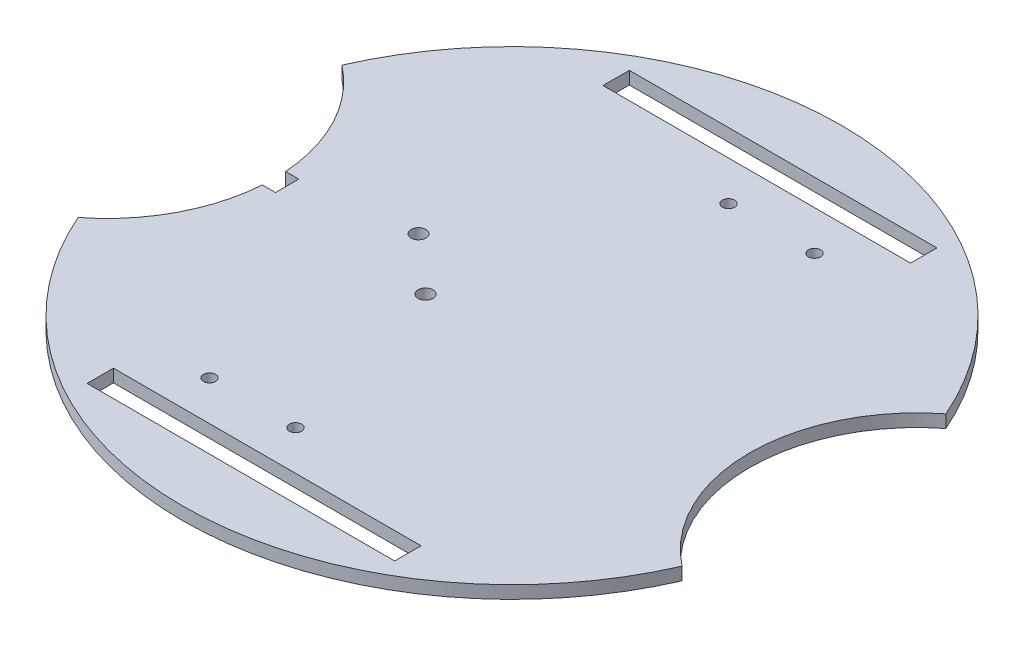
SolidWorks part; units mm, degrees
ref_plane "Front" through (0, 0, 0) normal (0, 0, 1) x (1, 0, 0)
ref_plane "Top" through (0, 0, 0) normal (0, 1, 0) x (1, 0, 0)
ref_plane "Right" through (0, 0, 0) normal (1, 0, 0) x (0, 0, -1)
sketch "Sketch1" plane through (0, 0, 0) normal (0, 1, 0) x (1, 0, 0)
  circle A0 centre (0, 0) radius 75
  dimension "D1" = 150
extrude "Boss-Extrude1" add sketch "Sketch1" along normal blind 2.9
sketch "Sketch2" plane through (0, 2.9, 0) normal (0, 1, 0) x (1, 0, 0)
  line L0 (-24.7, 25.6) -> (-24.7, -25.6) construction
  line L1 (-43.5, 28.4908) -> (-5.9, 28.4908) construction
  line L2 (-43.5, 28.4908) -> (-43.5, -22.7092) construction
  line L3 (-43.5, -22.7092) -> (-5.9, -22.7092) construction
  line L4 (-5.9, 28.4908) -> (-5.9, -22.7092) construction
  line L5 (-27.7, -22.7092) -> (-21.7, -22.7092) construction
  line L6 (-27.7, -22.7092) -> (-27.7, -42.7092) construction
  line L7 (-27.7, -42.7092) -> (-21.7, -42.7092)
  line L8 (-21.7, -22.7092) -> (-21.7, -42.7092) construction
  line L9 (24.7, 25.6) -> (24.7, -25.6) construction
  line L10 (5.9, 22.7092) -> (43.5, 22.7092) construction
  line L11 (5.9, 22.7092) -> (5.9, -28.4908) construction
  line L12 (5.9, -28.4908) -> (43.5, -28.4908) construction
  line L13 (43.5, 22.7092) -> (43.5, -28.4908) construction
  line L14 (0, 75) -> (0, -75) construction
  line L15 (21.7, 22.7092) -> (27.7, 22.7092) construction
  line L16 (21.7, 22.7092) -> (21.7, 42.7092) construction
  line L17 (21.7, 42.7092) -> (27.7, 42.7092)
  line L18 (27.7, 22.7092) -> (27.7, 42.7092) construction
  line L19 (-75, 0) -> (75, 0) construction
  line L20 (-54.0852, 0) -> (-54.0852, -59.9004) construction
  line L21 (-37.05, -42.7092) -> (-12.35, -42.7092) construction
  line L22 (-37.05, -42.7092) -> (-37.05, -52.7092) construction
  line L23 (-37.05, -52.7092) -> (-12.35, -52.7092) construction
  line L24 (-12.35, -42.7092) -> (-12.35, -52.7092) construction
  line L25 (12.35, 42.7092) -> (37.05, 42.7092) construction
  line L26 (12.35, 42.7092) -> (12.35, 52.7092) construction
  line L27 (12.35, 52.7092) -> (37.05, 52.7092) construction
  line L28 (37.05, 42.7092) -> (37.05, 52.7092) construction
  line L29 (-68.7285, 30.0232) -> (-92.1852, 0) construction
  line L30 (-68.7285, -30.0232) -> (-92.1852, 0) construction
  line L31 (-75, 0) -> (-75, -48.0416) construction
  line L32 (74.91, 3.6727) -> (70.3716, 3.6727) construction
  line L33 (70.3716, 3.6727) -> (70.3716, -3.6727) construction
  line L34 (70.3716, -3.6727) -> (74.91, -3.6727) construction
  line L35 (40.6357, -63.0376) -> (38.3665, -59.1072) construction
  line L36 (38.3665, -59.1072) -> (32.0051, -62.7799) construction
  line L37 (32.0051, -62.7799) -> (34.2744, -66.7103) construction
  line L38 (-34.2744, -66.7103) -> (-32.0051, -62.7799) construction
  line L39 (-32.0051, -62.7799) -> (-38.3665, -59.1072) construction
  line L40 (-38.3665, -59.1072) -> (-40.6357, -63.0376) construction
  line L41 (-74.91, -3.6727) -> (-70.3716, -3.6727) construction
  line L42 (-70.3716, -3.6727) -> (-70.3716, 3.6727) construction
  line L43 (-70.3716, 3.6727) -> (-74.91, 3.6727) construction
  line L44 (-40.6357, 63.0376) -> (-38.3665, 59.1072) construction
  line L45 (-38.3665, 59.1072) -> (-32.0051, 62.7799) construction
  line L46 (-32.0051, 62.7799) -> (-34.2744, 66.7103) construction
  line L47 (34.2744, 66.7103) -> (32.0051, 62.7799) construction
  line L48 (32.0051, 62.7799) -> (38.3665, 59.1072) construction
  line L49 (38.3665, 59.1072) -> (40.6357, 63.0376) construction
  line L51 (-35, -55.7092) -> (35, -55.7092)
  line L52 (-35, -55.7092) -> (-35, -61.7092)
  line L53 (-35, -61.7092) -> (35, -61.7092)
  line L54 (35, -55.7092) -> (35, -61.7092)
  line L55 (-35, 61.7092) -> (35, 61.7092)
  line L56 (-35, 61.7092) -> (-35, 55.7092)
  line L57 (-35, 55.7092) -> (35, 55.7092)
  line L58 (35, 61.7092) -> (35, 55.7092)
  circle A0 centre (0, 0) radius 75 construction
  circle A1 centre (-92.1852, 0) radius 38.1 construction
  arc A2 (-68.7285, 30.0232) -> (-68.7285, -30.0232) centre (-92.1852, 0) cw
  arc A3 (68.7285, 30.0232) -> (68.7285, -30.0232) centre (92.1852, 0) ccw
  circle A4 centre (-40.3, -14.3092) radius 1.6 construction
  circle A5 centre (-40.3, 4.8908) radius 1.6 construction
  circle A6 centre (-40.3, 24.0908) radius 1.6 construction
  circle A7 centre (-9.1, -14.3092) radius 1.6 construction
  circle A8 centre (-9.1, 4.8908) radius 1.6 construction
  circle A9 centre (-9.1, 24.0908) radius 1.6 construction
  circle A10 centre (40.3, 14.3092) radius 1.6 construction
  circle A11 centre (40.3, -4.8908) radius 1.6 construction
  circle A12 centre (40.3, -24.0908) radius 1.6 construction
  circle A13 centre (9.1, -24.0908) radius 1.6 construction
  circle A14 centre (9.1, -4.8908) radius 1.6 construction
  circle A15 centre (9.1, 14.3092) radius 1.6 construction
  circle A16 centre (-22.14, -46.7092) radius 1.4
  circle A17 centre (-22.14, -46.7092) radius 2.56 construction
  circle A18 centre (-2.56, -46.7092) radius 1.4
  circle A19 centre (-2.56, -46.7092) radius 2.56 construction
  circle A20 centre (22.14, 46.7092) radius 1.4
  circle A21 centre (22.14, 46.7092) radius 2.56 construction
  circle A22 centre (2.56, 46.7092) radius 1.4
  circle A23 centre (2.56, 46.7092) radius 2.56 construction
  point P39 (-68.7285, 30.0232)
  point P40 (-68.7285, -30.0232)
  point P74 (0, 0)
  circle M2 centre (0, 0) radius 75
  dimension "D10" = 76.2
  dimension "D16" = 6
  dimension "D17" = 3
  dimension "D18" = 19.2
  dimension "D19" = 3
  dimension "D20" = 31.2
  dimension "D21" = 3.2
  dimension "D22" = 3.2
  dimension "D24" = 8.4
  dimension "D25" = 31.2
  dimension "D26" = 2.8
  dimension "D27" = 5.12
  dimension "D28" = 4
  dimension "D29" = 5.12
  dimension "D30" = 2.8
  dimension "D31" = 5.12
  dimension "D32" = 2.8
  dimension "D34" = 5.12
  dimension "D35" = 2.8
  dimension "D1" = 37.6
  dimension "D2" = 51.2
  dimension "D3" = 6
  dimension "D4" = 20
  dimension "D5" = 37.6
  dimension "D6" = 51.2
  dimension "D7" = 6
  dimension "D8" = 20
  dimension "D9" = 24.7
  dimension "D11" = 10
  dimension "D12" = 24.7
  dimension "D13" = 10
  dimension "D14" = 24.7
  dimension "D15" = 104
  dimension "D33" = 4
  dimension "D36" = 11.8
  dimension "D37" = 70
  dimension "D38" = 6
  dimension "D39" = 70
  dimension "D40" = 6
  dimension "D41" = 3
  dimension "D42" = 8.4
  dimension "D23" = 3
extrude "Cut-Extrude1" cut sketch "Sketch2" against normal blind 10 contours A2 M2 | A3 M2 | A13 | A12 | A11 | A10 | A15 | A14 | A8 | A7 | A9 | A6 | A5 | A4 | A16 | A18 | A20 | A22 | L54 L51 L52 L53 | L58 L55 L56 L57
sketch "Sketch3" plane through (0, 2.9, 0) normal (0, 1, 0) x (1, 0, 0)
  line L0 (-54.0852, 0) -> (54.0852, 0) construction
  line L1 (-54.0852, 18.0725) -> (-54.0852, -19.408) construction
  line L2 (-54.1775, 2.65) -> (-51.1775, 2.65)
  line L3 (-51.1775, 2.65) -> (-51.1775, -2.65)
  line L4 (-51.1775, -2.65) -> (-54.1775, -2.65)
  arc A0 (-68.7285, -30.0232) -> (-68.7285, 30.0232) centre (-92.1852, 0) ccw construction
  arc A1 (68.7285, 30.0232) -> (68.7285, -30.0232) centre (92.1852, 0) ccw construction
  circle A2 centre (-26.7852, 5.5) radius 1.7
  circle A3 centre (-14.0852, -5.6) radius 1.7
  arc M11 (-68.7285, 30.0232) -> (-68.7285, -30.0232) centre (-92.1852, 0) cw
  dimension "D1" = 3.4
  dimension "D2" = 3.4
  dimension "D3" = 5.5
  dimension "D4" = 12.7
  dimension "D5" = 11.1
  dimension "D6" = 40
  dimension "D7" = 5.3
  dimension "D8" = 3
extrude "Cut-Extrude3" cut sketch "Sketch3" against normal blind 10 contours A2 | A3 | L4 L3 L2 M11
